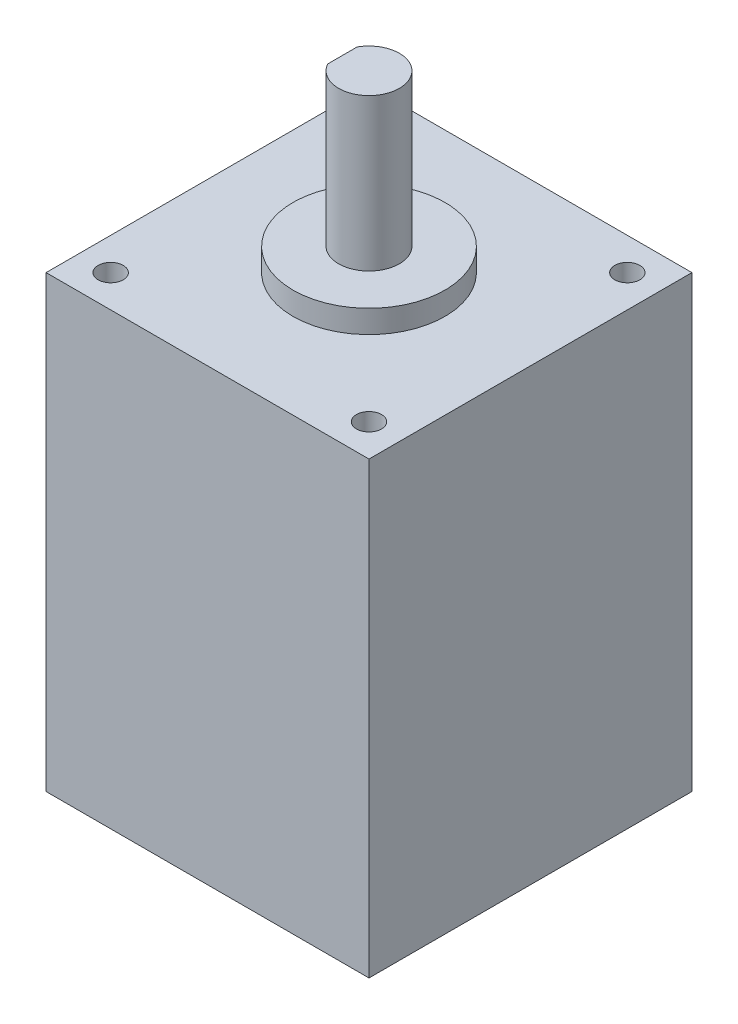
SolidWorks part; units mm, degrees
material "5052-O"
ref_plane "정면" through (0, 0, 0) normal (0, 0, 1) x (1, 0, 0)
ref_plane "윗면" through (0, 0, 0) normal (0, 1, 0) x (1, 0, 0)
ref_plane "우측면" through (0, 0, 0) normal (1, 0, 0) x (0, 0, -1)
ref_plane "평면1"
sketch "스케치1" plane through (0, 0, 0) normal (0, 1, 0) x (-1, 0, 0)
  line L0 (0, 0) -> (42.5, 0)
  line L1 (42.5, 0) -> (42.5, -42.5)
  line L2 (42.5, -42.5) -> (0, -42.5)
  line L3 (0, -42.5) -> (0, 0)
extrude "돌출1" add sketch "스케치1" along normal blind 59.15
sketch "스케치2" plane through (0, 59.15, 0) normal (0, 1, 0) x (-1, 0, 0)
  circle A0 centre (21.25, -21.25) radius 10
  dimension "D1" = 20
extrude "돌출2" add sketch "스케치2" along normal blind 3
sketch "스케치3" plane through (0, 62.15, 0) normal (0, 1, 0) x (-1, 0, 0)
  circle A0 centre (21.25, -21.25) radius 4
  dimension "D1" = 8
extrude "돌출3" add sketch "스케치3" along normal blind 20
hole_wizard "구멍3" positions "스케치5" profile "스케치4" tap size "M4" standard "ISO"
sketch "스케치5" plane through (0, 59.15, 0) normal (0, 1, 0) x (1, 0, 0)
  point P1 (-4.25, 38.25)
  point P2 (-4.25, 4.25)
  point P3 (-38.25, 4.25)
  point P4 (-38.25, 38.25)
cosmetic thread "나사산 표시1"
cosmetic thread "나사산 표시2"
sketch "스케치4" plane through (-4.25, 59.15, -38.25) normal (1, 0, 0) x (0, 0, 1)
  line L0 (0, 0) -> (0, 12.4914)
  line L1 (0, 12.4914) -> (1.65, 11.5)
  line L2 (1.65, 11.5) -> (1.65, 0)
  line L5 (1.65, 0) -> (0, 0)
  line L10 (0, 12.4914) -> (-1.65, 11.5) construction
  line L11 (0, -6.35) -> (0, 107.95) construction
  dimension "탭 드릴 지름" = 3.3
  dimension "탭 드릴 깊이" = 11.5
  dimension "드릴 각도" = 118
cosmetic thread "구멍 나사산1"
cosmetic thread "구멍 나사산3"
sketch "스케치6" plane through (0, 82.15, 0) normal (0, 1, 0) x (-1, 0, 0)
  line L0 (24.75, -19.3135) -> (24.75, -23.1865)
  arc A0 (24.75, -23.1865) -> (24.75, -19.3135) centre (21.25, -21.25) ccw
extrude "돌출4" cut sketch "스케치6" against normal blind 12
